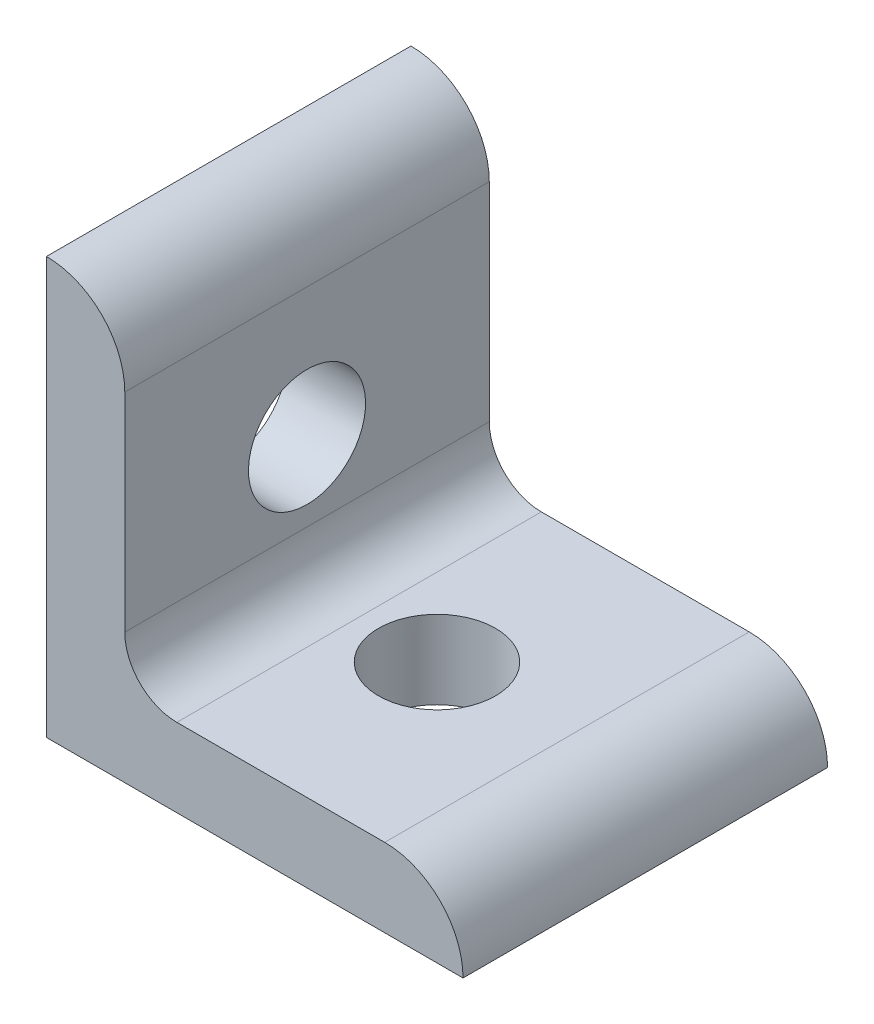
SolidWorks part; units mm, degrees
material "6061-T6 (SS)"
ref_plane "Front Plane" through (0, 0, 0) normal (0, 0, 1) x (1, 0, 0)
ref_plane "Top Plane" through (0, 0, 0) normal (0, 1, 0) x (1, 0, 0)
ref_plane "Right Plane" through (0, 0, 0) normal (1, 0, 0) x (0, 0, -1)
sketch "Sketch1" plane through (0, 0, 0) normal (0, 0, 1) x (1, 0, 0)
  line L0 (0, 0) -> (0, 25.4)
  line L1 (4.7752, 20.6248) -> (4.7752, 25.4) construction
  line L2 (4.7752, 20.6248) -> (4.7752, 7.9502)
  line L3 (7.9502, 4.7752) -> (20.6248, 4.7752)
  line L4 (4.7752, 25.4) -> (0, 25.4) construction
  line L5 (25.4, 0) -> (0, 0)
  line L6 (20.6248, 4.7752) -> (25.4, 4.7752) construction
  line L7 (25.4, 4.7752) -> (25.4, 0) construction
  arc A0 (4.7752, 20.6248) -> (0, 25.4) centre (0, 20.6248) ccw
  arc A1 (25.4, 0) -> (20.6248, 4.7752) centre (20.6248, 0) ccw
  arc A2 (4.7752, 7.9502) -> (7.9502, 4.7752) centre (7.9502, 7.9502) ccw
  point P10 (4.7752, 23.0124)
  dimension "E" = 3.175
  dimension "D" = 4.7752
  dimension "C" = 25.4
  dimension "B" = 25.4
extrude "Boss-Extrude1" add sketch "Sketch1" along normal mid plane 22.225
sketch "Sketch2" plane through (0, 0, 0) normal (0, 1, 0) x (1, 0, 0)
  line L0 (0, 0) -> (12.7, 0) construction
  circle A0 centre (12.7, 0) radius 3.5687
extrude "Cut-Extrude1" cut sketch "Sketch2" along normal through all
sketch "Sketch3" plane through (0, 0, 0) normal (1, 0, 0) x (0, 0, -1)
  line L0 (0, 0) -> (0, 12.7) construction
  circle A0 centre (0, 12.7) radius 3.5687
  dimension "D1" = 12.7
extrude "Cut-Extrude2" cut sketch "Sketch3" along normal through all
equation "\"E@Sketch3\" = \"E@Sketch2\""
equation "\"D1@Sketch3\" = \"D1@Sketch2\""
